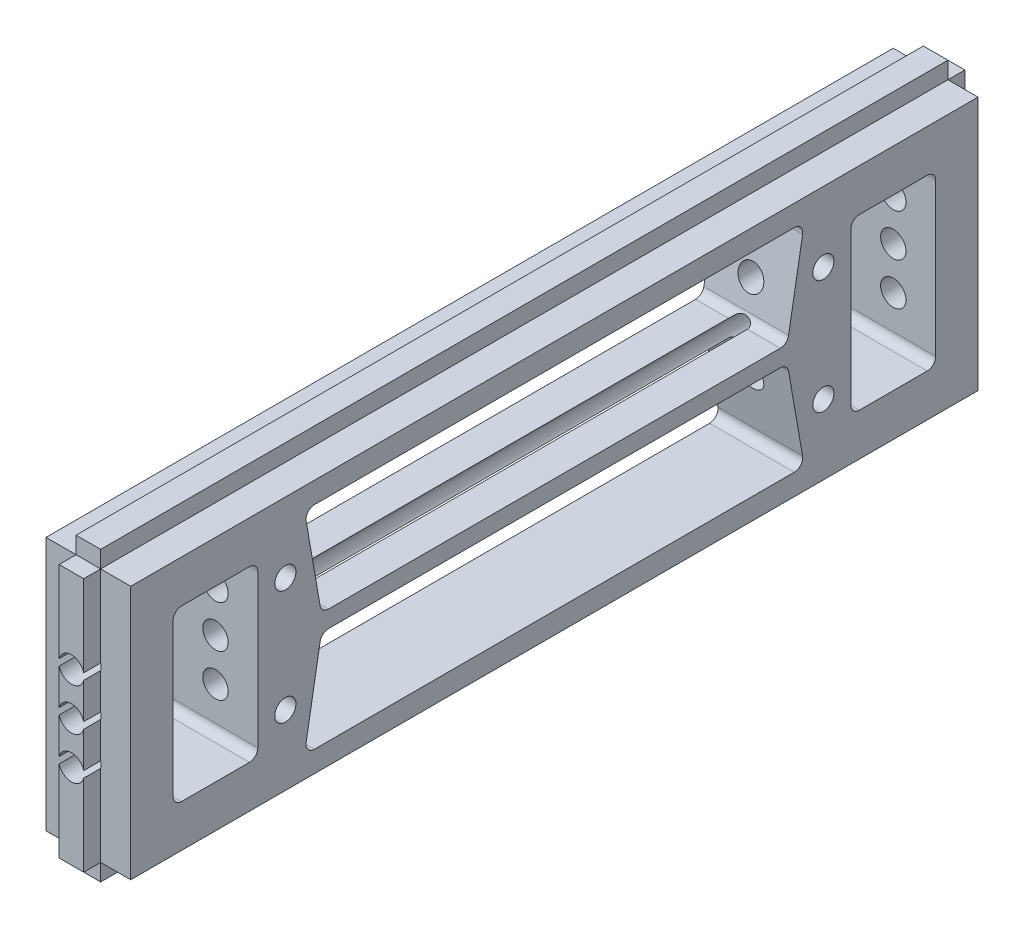
SolidWorks part; units mm, degrees
ref_plane "Front Plane" through (0, 0, 0) normal (0, 0, 1) x (1, 0, 0)
ref_plane "Top Plane" through (0, 0, 0) normal (0, 1, 0) x (1, 0, 0)
ref_plane "Right Plane" through (0, 0, 0) normal (1, 0, 0) x (0, 0, -1)
sketch "Sketch1" plane through (0, 0, 0) normal (0, 0, 1) x (1, 0, 0)
  line L0 (-5, -15) -> (-1.45, -15)
  line L1 (5, -15) -> (5, 15)
  line L2 (5, 15) -> (1.45, 15)
  line L3 (1.45, 15) -> (1.45, 17)
  line L4 (1.45, 17) -> (-1.45, 17)
  line L5 (-1.45, 17) -> (-1.45, 15)
  line L6 (-1.45, 15) -> (-5, 15)
  line L7 (-5, 15) -> (-5, -15)
  line L8 (-1.45, -15) -> (-1.45, -17)
  line L9 (-1.45, -17) -> (1.45, -17)
  line L10 (1.45, -17) -> (1.45, -15)
  line L11 (1.45, -15) -> (5, -15)
  point P9 (0, 17)
  point P14 (-5, 0)
  dimension "D1" = 10
  dimension "D2" = 2.9
  dimension "D3" = 30
  dimension "D4" = 2
  dimension "D5" = 2
extrude "MakerBeamFix" add sketch "Sketch1" along normal mid plane 100
sketch "Sketch4" plane through (-5, 0, 0) normal (-1, 0, 0) x (0, 0, 1)
  line L1 (-29.5, 12.5) -> (29.5, 12.5)
  line L2 (-29.5, 12.5) -> (-27.5, 1)
  line L3 (-27.5, 1) -> (27.5, 1)
  line L4 (29.5, 12.5) -> (27.5, 1)
  line L5 (50, 15) -> (-50, 15) construction
  circle A0 centre (-31.75, 6.75) radius 1.25
  circle A1 centre (31.75, 6.75) radius 1.25
  point P8 (-28.5, 6.75)
  point P11 (0, 1)
  dimension "D5" = 2.5
  dimension "D1" = 31.75
  dimension "D2" = 31.75
  dimension "D3" = 11.5
  dimension "D4" = 59
  dimension "D6" = 55
  dimension "D7" = 2.5
extrude "HoleForHartingConnector" cut sketch "Sketch4" against normal through all
fillet "Fillet1" radius 1 4 edges at (0, 12.5, -29.5) (0, 1, -27.5) (0, 1, 27.5) (0, 12.5, 29.5)
mirror "Mirror1" about plane through (0, 0, 0) normal (0, 1, 0) of "Fillet1", "HoleForHartingConnector"
sketch "Sketch5" plane through (0, 0, 50) normal (0, 0, 1) x (1, 0, 0)
  line L1 (-1.45, 15) -> (1.45, 15)
  line L2 (-1.45, 15) -> (-1.45, -15)
  line L3 (-1.45, -15) -> (1.45, -15)
  line L4 (1.45, 15) -> (1.45, -15)
extrude "MakerBeamFixLeft" add sketch "Sketch5" along normal blind 2
sketch "Sketch6" plane through (0, 0, -50) normal (0, 0, -1) x (-1, 0, 0)
  line L1 (-1.45, 15) -> (1.45, 15)
  line L2 (-1.45, 15) -> (-1.45, -15)
  line L3 (-1.45, -15) -> (1.45, -15)
  line L4 (1.45, 15) -> (1.45, -15)
extrude "MakerBeamFixRight" add sketch "Sketch6" along normal blind 2
sketch "Sketch7" plane through (-5, 0, 0) normal (-1, 0, 0) x (0, 0, 1)
  line L0 (50, -15) -> (50, 15) construction
  line L1 (45, 10) -> (35, 10)
  line L2 (45, 10) -> (45, -10)
  line L3 (45, -10) -> (35, -10)
  line L4 (35, 10) -> (35, -10)
  line L5 (50, 15) -> (-50, 15) construction
  line L6 (-50, -15) -> (-50, 15) construction
  line L7 (-35, 10) -> (-45, 10)
  line L8 (-35, 10) -> (-35, -10)
  line L9 (-35, -10) -> (-45, -10)
  line L10 (-45, 10) -> (-45, -10)
  dimension "D1" = 5
  dimension "D2" = 5
  dimension "D3" = 20
  dimension "D4" = 10
  dimension "D5" = 5
extrude "MakerBeamSideHolesForScrew" cut sketch "Sketch7" against normal through all
sketch "Sketch8" plane through (0, 0, 52) normal (0, 0, 1) x (1, 0, 0)
  circle A0 centre (0, -5) radius 1.5
  circle A1 centre (0, 0) radius 1.5
  circle A2 centre (0, 5) radius 1.5
  point P7 (0, 0)
  dimension "D1" = 3
  dimension "D2" = 5
  dimension "D3" = 5
extrude "MakerBeamSideHoles" cut sketch "Sketch8" against normal up to surface (97 mm away)
mirror "MakerBeamSideHolesMirror" about plane through (0, 0, 0) normal (0, 0, 1) of "MakerBeamSideHoles"
fillet "Fillet2" radius 1 8 edges at (0, -10, 45) (0, -10, 35) (0, 10, 35) (0, 10, 45) (0, -10, -35) (0, 10, -45) (0, 10, -35) (0, -10, -45)
